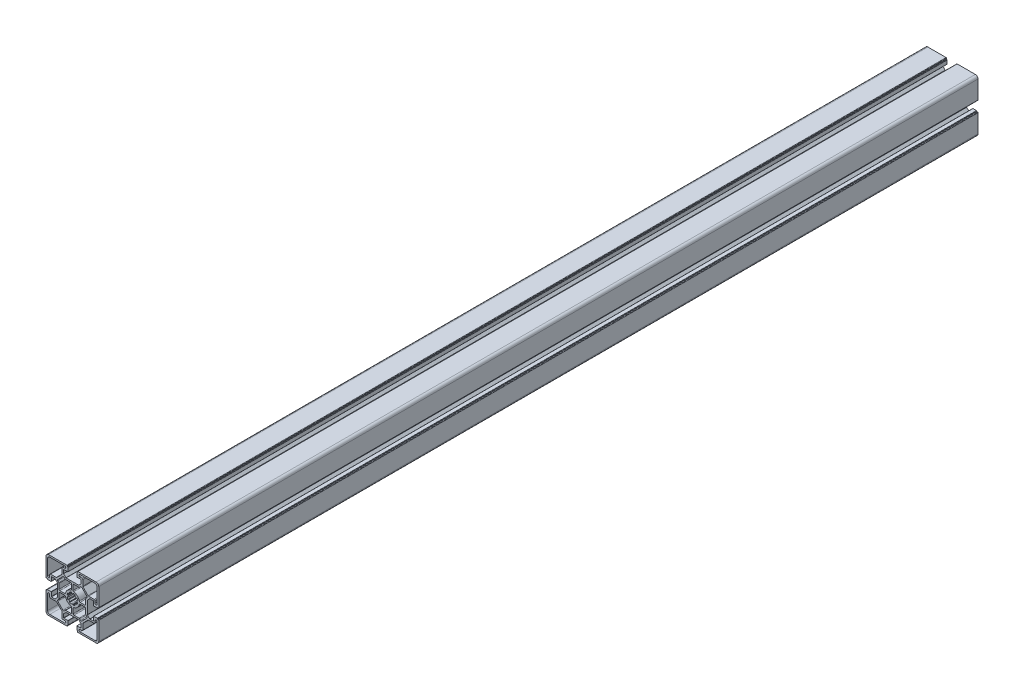
SolidWorks part; units mm, degrees
material "АД31 ГОСТ 4784-97"
ref_plane "Спереди" through (0, 0, 0) normal (0, 0, 1) x (1, 0, 0)
ref_plane "Сверху" through (0, 0, 0) normal (0, 1, 0) x (1, 0, 0)
ref_plane "Справа" through (0, 0, 0) normal (1, 0, 0) x (0, 0, -1)
sketch "Эскиз1" plane through (0, 0, 0) normal (0, 0, 1) x (1, 0, 0)
  line L0 (16.1477, -4.2469) -> (16.1477, 1.4345)
  line L1 (17.495, 3.196) -> (16.4406, 2.1416)
  line L2 (17.495, 4.6102) -> (11.7048, 10.4004)
  line L3 (9.2362, 9.346) -> (10.2906, 10.4004)
  line L4 (8.529, 9.0531) -> (2.8477, 9.0531)
  line L5 (1.8477, 2.6503) -> (1.8477, 8.0531)
  line L6 (15.1477, -5.2469) -> (9.7448, -5.2469)
  line L7 (25.7477, 5.7031) -> (19.3619, 5.7031)
  line L8 (18.6548, 5.996) -> (13.0906, 11.5602)
  line L9 (12.7977, 12.2673) -> (12.7977, 18.6531)
  line L10 (11.7977, 19.6531) -> (9.6477, 19.6531)
  line L11 (26.6477, 22.0531) -> (9.6477, 22.0531)
  line L12 (29.1477, 2.5531) -> (29.1477, 19.5531)
  line L13 (26.7477, 2.5531) -> (26.7477, 4.7031)
  line L14 (6.4406, -5.1783) -> (5.8717, -5.2786)
  line L15 (5.0434, -3.279) -> (5.5166, -2.9477)
  line L16 (4.1469, -1.578) -> (3.8156, -2.0511)
  line L17 (1.9162, -0.654) -> (1.8159, -1.2228)
  line L18 (10.9391, 13.5945) -> (8.2563, 10.9117)
  line L19 (10.9977, 13.736) -> (10.9977, 17.6531)
  line L20 (-16.0523, -13.314) -> (-16.0523, 1.0203)
  line L21 (-16.1109, 1.1617) -> (-18.7937, 3.8445)
  line L22 (-22.8523, 3.9031) -> (-18.9352, 3.9031)
  line L23 (-23.0523, -0.9469) -> (-23.0523, 3.7031)
  line L24 (-23.2523, -1.1469) -> (-27.2523, -1.1469)
  line L25 (-27.5523, -0.8469) -> (-27.5523, -0.6469)
  line L26 (-28.5523, -0.3469) -> (-27.8523, -0.3469)
  line L27 (-29.0523, 0.1531) -> (-29.0523, 20.8531)
  line L28 (-26.0523, 23.8531) -> (-5.3523, 23.8531)
  line L29 (-4.8523, 22.6531) -> (-4.8523, 23.3531)
  line L30 (-4.5523, 22.3531) -> (-4.3523, 22.3531)
  line L31 (-4.0523, 18.0531) -> (-4.0523, 22.0531)
  line L32 (-8.9023, 17.8531) -> (-4.2523, 17.8531)
  line L33 (-9.1023, 13.736) -> (-9.1023, 17.6531)
  line L34 (-9.0438, 13.5945) -> (-6.3609, 10.9117)
  line L35 (-6.2195, 10.8531) -> (8.1148, 10.8531)
  line L36 (10.7977, 17.8531) -> (6.1477, 17.8531)
  line L37 (5.9477, 18.0531) -> (5.9477, 22.0531)
  line L38 (6.4477, 22.3531) -> (6.2477, 22.3531)
  line L39 (6.7477, 22.6531) -> (6.7477, 23.3531)
  line L40 (27.9477, 23.8531) -> (7.2477, 23.8531)
  line L41 (30.9477, 0.1531) -> (30.9477, 20.8531)
  line L42 (30.4477, -0.3469) -> (29.7477, -0.3469)
  line L43 (29.4477, -0.8469) -> (29.4477, -0.6469)
  line L44 (25.1477, -1.1469) -> (29.1477, -1.1469)
  line L45 (24.9477, -0.9469) -> (24.9477, 3.7031)
  line L46 (24.7477, 3.9031) -> (20.8305, 3.9031)
  line L47 (18.0063, 1.1617) -> (20.6891, 3.8445)
  line L48 (17.9477, -13.314) -> (17.9477, 1.0203)
  line L49 (-14.2523, -8.0469) -> (-14.2523, -13.7282)
  line L50 (-15.5996, -15.4897) -> (-14.5452, -14.4353)
  line L51 (-15.5996, -16.904) -> (-9.8094, -22.6942)
  line L52 (-7.3408, -21.6397) -> (-8.3952, -22.6942)
  line L53 (-6.6337, -21.3469) -> (-0.9523, -21.3469)
  line L54 (0.0477, -14.944) -> (0.0477, -20.3469)
  line L55 (-13.2523, -7.0469) -> (-7.8495, -7.0469)
  line L56 (-23.8523, -17.9969) -> (-17.4665, -17.9969)
  line L57 (-16.7594, -18.2898) -> (-11.1952, -23.854)
  line L58 (-10.9023, -24.5611) -> (-10.9023, -30.9469)
  line L59 (-9.9023, -31.9469) -> (-7.7523, -31.9469)
  line L60 (-0.0209, -0.654) -> (0.0794, -1.2228)
  line L61 (-2.2515, -1.578) -> (-1.9202, -2.0511)
  line L62 (-3.1481, -3.279) -> (-3.6212, -2.9477)
  line L63 (-4.5452, -5.1783) -> (-3.9764, -5.2786)
  line L64 (-24.7523, -34.3469) -> (-7.7523, -34.3469)
  line L65 (-27.2523, -14.8469) -> (-27.2523, -31.8469)
  line L66 (-24.8523, -14.8469) -> (-24.8523, -16.9969)
  line L67 (-4.5452, -7.1154) -> (-3.9764, -7.0151)
  line L68 (-3.1481, -9.0147) -> (-3.6212, -9.3461)
  line L69 (-2.2515, -10.7158) -> (-1.9202, -10.2426)
  line L70 (-0.0209, -11.6397) -> (0.0794, -11.0709)
  line L71 (18.0063, -13.4554) -> (20.6891, -16.1383)
  line L72 (24.7477, -16.1968) -> (20.8305, -16.1968)
  line L73 (24.9477, -11.3468) -> (24.9477, -15.9968)
  line L74 (25.1477, -11.1468) -> (29.1477, -11.1468)
  line L75 (29.4477, -11.4468) -> (29.4477, -11.6468)
  line L76 (30.4477, -11.9468) -> (29.7477, -11.9468)
  line L77 (30.9477, -12.4468) -> (30.9477, -33.1468)
  line L78 (27.9477, -36.1468) -> (7.2477, -36.1468)
  line L79 (6.7477, -34.9468) -> (6.7477, -35.6468)
  line L80 (6.4477, -34.6468) -> (6.2477, -34.6468)
  line L81 (5.9477, -30.3468) -> (5.9477, -34.3468)
  line L82 (10.7977, -30.1468) -> (6.1477, -30.1468)
  line L83 (-6.2195, -23.1468) -> (8.1148, -23.1468)
  line L84 (-9.0438, -25.8883) -> (-6.3609, -23.2054)
  line L85 (-9.1023, -26.0297) -> (-9.1023, -29.9468)
  line L86 (-8.9023, -30.1468) -> (-4.2523, -30.1468)
  line L87 (-4.0523, -30.3468) -> (-4.0523, -34.3468)
  line L88 (-4.5523, -34.6468) -> (-4.3523, -34.6468)
  line L89 (-4.8523, -34.9468) -> (-4.8523, -35.6468)
  line L90 (-26.0523, -36.1468) -> (-5.3523, -36.1468)
  line L91 (-29.0523, -12.4468) -> (-29.0523, -33.1468)
  line L92 (-28.5523, -11.9468) -> (-27.8523, -11.9468)
  line L93 (-27.5523, -11.4468) -> (-27.5523, -11.6468)
  line L94 (-23.2523, -11.1468) -> (-27.2523, -11.1468)
  line L95 (-23.0523, -11.3468) -> (-23.0523, -15.9968)
  line L96 (-22.8523, -16.1968) -> (-18.9352, -16.1968)
  line L97 (-16.1109, -13.4554) -> (-18.7937, -16.1383)
  line L98 (10.9977, -26.0297) -> (10.9977, -29.9468)
  line L99 (10.9391, -25.8883) -> (8.2563, -23.2054)
  line L100 (1.9162, -11.6397) -> (1.8159, -11.0709)
  line L101 (4.1469, -10.7158) -> (3.8156, -10.2426)
  line L102 (5.0434, -9.0147) -> (5.5166, -9.3461)
  line L103 (6.4406, -7.1154) -> (5.8717, -7.0151)
  line L104 (-24.8523, 2.5531) -> (-24.8523, 4.7031)
  line L105 (-27.2523, 2.5531) -> (-27.2523, 19.5531)
  line L106 (-24.7523, 22.0531) -> (-7.7523, 22.0531)
  line L107 (-9.9023, 19.6531) -> (-7.7523, 19.6531)
  line L108 (-10.9023, 12.2673) -> (-10.9023, 18.6531)
  line L109 (-16.7594, 5.996) -> (-11.1952, 11.5602)
  line L110 (-23.8523, 5.7031) -> (-17.4665, 5.7031)
  line L111 (26.7477, -14.8469) -> (26.7477, -16.9969)
  line L112 (29.1477, -14.8469) -> (29.1477, -31.8469)
  line L113 (26.6477, -34.3469) -> (9.6477, -34.3469)
  line L114 (11.7977, -31.9469) -> (9.6477, -31.9469)
  line L115 (12.7977, -24.5611) -> (12.7977, -30.9469)
  line L116 (18.6548, -18.2898) -> (13.0906, -23.854)
  line L117 (25.7477, -17.9969) -> (19.3619, -17.9969)
  line L118 (-13.2523, -5.2469) -> (-7.8495, -5.2469)
  line L119 (0.0477, 2.6503) -> (0.0477, 8.0531)
  line L120 (-6.6337, 9.0531) -> (-0.9523, 9.0531)
  line L121 (-7.3408, 9.346) -> (-8.3952, 10.4004)
  line L122 (-15.5996, 4.6102) -> (-9.8094, 10.4004)
  line L123 (-15.5996, 3.196) -> (-14.5452, 2.1416)
  line L124 (-14.2523, -4.2469) -> (-14.2523, 1.4345)
  line L125 (15.1477, -7.0469) -> (9.7448, -7.0469)
  line L126 (1.8477, -14.944) -> (1.8477, -20.3469)
  line L127 (8.529, -21.3469) -> (2.8477, -21.3469)
  line L128 (9.2362, -21.6397) -> (10.2906, -22.6942)
  line L129 (17.495, -16.904) -> (11.7048, -22.6942)
  line L130 (17.495, -15.4897) -> (16.4406, -14.4353)
  line L131 (16.1477, -8.0469) -> (16.1477, -13.7282)
  line L132 (0.9477, -6.1469) -> (0.9477, -46.3575) construction
  line L133 (0.9477, -6.1469) -> (0.9477, 45.0283) construction
  line L134 (0.9477, -6.1469) -> (50.4915, -6.1469) construction
  line L135 (0.9477, -6.1469) -> (-49.7618, -6.1469) construction
  arc A0 (16.1477, -4.2469) -> (15.1477, -5.2469) centre (15.1477, -4.2469) cw
  arc A1 (16.1477, 1.4345) -> (16.4406, 2.1416) centre (17.1477, 1.4345) cw
  arc A2 (17.495, 4.6102) -> (17.495, 3.196) centre (16.7879, 3.9031) cw
  arc A3 (10.2906, 10.4004) -> (11.7048, 10.4004) centre (10.9977, 9.6933) cw
  arc A4 (9.2362, 9.346) -> (8.529, 9.0531) centre (8.529, 10.0531) cw
  arc A5 (1.8477, 8.0531) -> (2.8477, 9.0531) centre (2.8477, 8.0531) cw
  arc A6 (2.6366, 1.6728) -> (1.8477, 2.6503) centre (2.8477, 2.6503) cw
  arc A7 (2.6366, 1.6728) -> (8.7674, -4.458) centre (0.9477, -6.1469) cw
  arc A8 (9.7448, -5.2469) -> (8.7674, -4.458) centre (9.7448, -4.2469) cw
  arc A9 (25.7477, 5.7031) -> (26.7477, 4.7031) centre (25.7477, 4.7031) cw
  arc A10 (19.3619, 5.7031) -> (18.6548, 5.996) centre (19.3619, 6.7031) cw
  arc A11 (13.0906, 11.5602) -> (12.7977, 12.2673) centre (13.7977, 12.2673) cw
  arc A12 (11.7977, 19.6531) -> (12.7977, 18.6531) centre (11.7977, 18.6531) cw
  arc A13 (9.6477, 19.6531) -> (9.6477, 22.0531) centre (9.6477, 20.8531) cw
  arc A14 (26.6477, 22.0531) -> (29.1477, 19.5531) centre (26.6477, 19.5531) cw
  arc A15 (29.1477, 2.5531) -> (26.7477, 2.5531) centre (27.9477, 2.5531) cw
  arc A16 (0.9477, -1.1469) -> (1.8159, -1.2228) centre (0.9477, -6.1469) cw
  arc A17 (5.8717, -5.2786) -> (5.9477, -6.1469) centre (0.9477, -6.1469) cw
  arc A18 (6.8364, -4.5555) -> (6.4406, -5.1783) centre (6.3537, -4.6859) cw
  arc A19 (6.2369, -3.1082) -> (6.8364, -4.5555) centre (0.9477, -6.1469) cw
  arc A20 (-16.0523, 1.0203) -> (-16.1109, 1.1617) centre (-16.2523, 1.0203) ccw
  arc A21 (-18.7937, 3.8445) -> (-18.9352, 3.9031) centre (-18.9352, 3.7031) ccw
  arc A22 (-22.8523, 3.9031) -> (-23.0523, 3.7031) centre (-22.8523, 3.7031) ccw
  arc A23 (-23.2523, -1.1469) -> (-23.0523, -0.9469) centre (-23.2523, -0.9469) ccw
  arc A24 (-27.5523, -0.8469) -> (-27.2523, -1.1469) centre (-27.2523, -0.8469) ccw
  arc A25 (-27.5523, -0.6469) -> (-27.8523, -0.3469) centre (-27.8523, -0.6469) ccw
  arc A26 (-29.0523, 0.1531) -> (-28.5523, -0.3469) centre (-28.5523, 0.1531) ccw
  arc A27 (-26.0523, 23.8531) -> (-29.0523, 20.8531) centre (-26.0523, 20.8531) ccw
  arc A28 (-4.8523, 23.3531) -> (-5.3523, 23.8531) centre (-5.3523, 23.3531) ccw
  arc A29 (-4.8523, 22.6531) -> (-4.5523, 22.3531) centre (-4.5523, 22.6531) ccw
  arc A30 (-4.0523, 22.0531) -> (-4.3523, 22.3531) centre (-4.3523, 22.0531) ccw
  arc A31 (-4.2523, 17.8531) -> (-4.0523, 18.0531) centre (-4.2523, 18.0531) ccw
  arc A32 (-8.9023, 17.8531) -> (-9.1023, 17.6531) centre (-8.9023, 17.6531) ccw
  arc A33 (-9.1023, 13.736) -> (-9.0438, 13.5945) centre (-8.9023, 13.736) ccw
  arc A34 (-6.3609, 10.9117) -> (-6.2195, 10.8531) centre (-6.2195, 11.0531) ccw
  arc A35 (5.5166, -2.9477) -> (6.2369, -3.1082) centre (5.8034, -3.3572) cw
  arc A36 (3.8156, -2.0511) -> (5.0434, -3.279) centre (0.9477, -6.1469) cw
  arc A37 (3.9864, -0.8576) -> (4.1469, -1.578) centre (3.7373, -1.2912) cw
  arc A38 (2.5391, -0.2581) -> (3.9864, -0.8576) centre (0.9477, -6.1469) cw
  arc A39 (1.9162, -0.654) -> (2.5391, -0.2581) centre (2.4086, -0.7408) cw
  arc A40 (8.2563, 10.9117) -> (8.1148, 10.8531) centre (8.1148, 11.0531) cw
  arc A41 (10.9977, 13.736) -> (10.9391, 13.5945) centre (10.7977, 13.736) cw
  arc A42 (10.7977, 17.8531) -> (10.9977, 17.6531) centre (10.7977, 17.6531) cw
  arc A43 (6.1477, 17.8531) -> (5.9477, 18.0531) centre (6.1477, 18.0531) cw
  arc A44 (5.9477, 22.0531) -> (6.2477, 22.3531) centre (6.2477, 22.0531) cw
  arc A45 (6.7477, 22.6531) -> (6.4477, 22.3531) centre (6.4477, 22.6531) cw
  arc A46 (6.7477, 23.3531) -> (7.2477, 23.8531) centre (7.2477, 23.3531) cw
  arc A47 (27.9477, 23.8531) -> (30.9477, 20.8531) centre (27.9477, 20.8531) cw
  arc A48 (30.9477, 0.1531) -> (30.4477, -0.3469) centre (30.4477, 0.1531) cw
  arc A49 (29.4477, -0.6469) -> (29.7477, -0.3469) centre (29.7477, -0.6469) cw
  arc A50 (29.4477, -0.8469) -> (29.1477, -1.1469) centre (29.1477, -0.8469) cw
  arc A51 (25.1477, -1.1469) -> (24.9477, -0.9469) centre (25.1477, -0.9469) cw
  arc A52 (24.7477, 3.9031) -> (24.9477, 3.7031) centre (24.7477, 3.7031) cw
  arc A53 (20.6891, 3.8445) -> (20.8305, 3.9031) centre (20.8305, 3.7031) cw
  arc A54 (17.9477, 1.0203) -> (18.0063, 1.1617) centre (18.1477, 1.0203) cw
  arc A55 (-14.2523, -8.0469) -> (-13.2523, -7.0469) centre (-13.2523, -8.0469) cw
  arc A56 (-14.2523, -13.7282) -> (-14.5452, -14.4353) centre (-15.2523, -13.7282) cw
  arc A57 (-15.5996, -16.904) -> (-15.5996, -15.4897) centre (-14.8925, -16.1969) cw
  arc A58 (-8.3952, -22.6942) -> (-9.8094, -22.6942) centre (-9.1023, -21.9871) cw
  arc A59 (-7.3408, -21.6397) -> (-6.6337, -21.3469) centre (-6.6337, -22.3469) cw
  arc A60 (-0.0209, -0.654) -> (-0.6437, -0.2581) centre (-0.5133, -0.7408) ccw
  arc A61 (-0.6437, -0.2581) -> (-2.091, -0.8576) centre (0.9477, -6.1469) ccw
  arc A62 (-2.091, -0.8576) -> (-2.2515, -1.578) centre (-1.842, -1.2912) ccw
  arc A63 (-1.9202, -2.0511) -> (-3.1481, -3.279) centre (0.9477, -6.1469) ccw
  arc A64 (-3.6212, -2.9477) -> (-4.3416, -3.1082) centre (-3.908, -3.3572) ccw
  arc A65 (-4.3416, -3.1082) -> (-4.9411, -4.5555) centre (0.9477, -6.1469) ccw
  arc A66 (-4.9411, -4.5555) -> (-4.5452, -5.1783) centre (-4.4584, -4.6859) ccw
  arc A67 (-3.9764, -5.2786) -> (-4.0523, -6.1469) centre (0.9477, -6.1469) ccw
  arc A68 (0.0477, -20.3469) -> (-0.9523, -21.3469) centre (-0.9523, -20.3469) cw
  arc A69 (-0.7412, -13.9666) -> (0.0477, -14.944) centre (-0.9523, -14.944) cw
  arc A70 (-0.7412, -13.9666) -> (-6.872, -7.8357) centre (0.9477, -6.1469) cw
  arc A71 (-7.8495, -7.0469) -> (-6.872, -7.8357) centre (-7.8495, -8.0469) cw
  arc A72 (-23.8523, -17.9969) -> (-24.8523, -16.9969) centre (-23.8523, -16.9969) cw
  arc A73 (-17.4665, -17.9969) -> (-16.7594, -18.2898) centre (-17.4665, -18.9969) cw
  arc A74 (-11.1952, -23.854) -> (-10.9023, -24.5611) centre (-11.9023, -24.5611) cw
  arc A75 (-9.9023, -31.9469) -> (-10.9023, -30.9469) centre (-9.9023, -30.9469) cw
  arc A76 (-7.7523, -31.9469) -> (-7.7523, -34.3469) centre (-7.7523, -33.1469) cw
  arc A77 (-24.7523, -34.3469) -> (-27.2523, -31.8469) centre (-24.7523, -31.8469) cw
  arc A78 (-27.2523, -14.8469) -> (-24.8523, -14.8469) centre (-26.0523, -14.8469) cw
  arc A79 (0.9477, -11.1469) -> (0.0794, -11.0709) centre (0.9477, -6.1468) cw
  arc A80 (-3.9764, -7.0151) -> (-4.0523, -6.1469) centre (0.9477, -6.1468) cw
  arc A81 (-4.9411, -7.7383) -> (-4.5452, -7.1154) centre (-4.4584, -7.6078) cw
  arc A82 (-4.3416, -9.1856) -> (-4.9411, -7.7383) centre (0.9477, -6.1469) cw
  arc A83 (-3.6212, -9.3461) -> (-4.3416, -9.1856) centre (-3.908, -8.9365) cw
  arc A84 (-1.9202, -10.2426) -> (-3.1481, -9.0147) centre (0.9477, -6.1468) cw
  arc A85 (-2.091, -11.4361) -> (-2.2515, -10.7158) centre (-1.842, -11.0026) cw
  arc A86 (-0.6437, -12.0356) -> (-2.091, -11.4361) centre (0.9477, -6.1469) cw
  arc A87 (-0.0209, -11.6397) -> (-0.6437, -12.0356) centre (-0.5133, -11.5529) cw
  arc A88 (17.9477, -13.314) -> (18.0063, -13.4554) centre (18.1477, -13.314) ccw
  arc A89 (20.6891, -16.1383) -> (20.8305, -16.1968) centre (20.8305, -15.9968) ccw
  arc A90 (24.7477, -16.1968) -> (24.9477, -15.9968) centre (24.7477, -15.9968) ccw
  arc A91 (0.9477, -1.1469) -> (0.0794, -1.2228) centre (0.9477, -6.1469) ccw
  arc A92 (25.1477, -11.1468) -> (24.9477, -11.3468) centre (25.1477, -11.3468) ccw
  arc A93 (29.4477, -11.4468) -> (29.1477, -11.1468) centre (29.1477, -11.4468) ccw
  arc A94 (29.4477, -11.6468) -> (29.7477, -11.9468) centre (29.7477, -11.6468) ccw
  arc A95 (30.9477, -12.4468) -> (30.4477, -11.9468) centre (30.4477, -12.4468) ccw
  arc A96 (27.9477, -36.1468) -> (30.9477, -33.1468) centre (27.9477, -33.1468) ccw
  arc A97 (6.7477, -35.6468) -> (7.2477, -36.1468) centre (7.2477, -35.6468) ccw
  arc A98 (6.7477, -34.9468) -> (6.4477, -34.6468) centre (6.4477, -34.9468) ccw
  arc A99 (5.9477, -34.3468) -> (6.2477, -34.6468) centre (6.2477, -34.3468) ccw
  arc A100 (6.1477, -30.1468) -> (5.9477, -30.3468) centre (6.1477, -30.3468) ccw
  arc A101 (10.7977, -30.1468) -> (10.9977, -29.9468) centre (10.7977, -29.9468) ccw
  arc A102 (10.9977, -26.0297) -> (10.9391, -25.8883) centre (10.7977, -26.0297) ccw
  arc A103 (8.2563, -23.2054) -> (8.1148, -23.1468) centre (8.1148, -23.3468) ccw
  arc A104 (1.9162, -11.6397) -> (2.5391, -12.0356) centre (2.4086, -11.5529) ccw
  arc A105 (2.5391, -12.0356) -> (3.9864, -11.4361) centre (0.9477, -6.1469) ccw
  arc A106 (3.9864, -11.4361) -> (4.1469, -10.7158) centre (3.7373, -11.0026) ccw
  arc A107 (3.8156, -10.2426) -> (5.0434, -9.0147) centre (0.9477, -6.1468) ccw
  arc A108 (5.5166, -9.3461) -> (6.2369, -9.1856) centre (5.8034, -8.9365) ccw
  arc A109 (-6.3609, -23.2054) -> (-6.2195, -23.1468) centre (-6.2195, -23.3468) cw
  arc A110 (-9.1023, -26.0297) -> (-9.0438, -25.8883) centre (-8.9023, -26.0297) cw
  arc A111 (-8.9023, -30.1468) -> (-9.1023, -29.9468) centre (-8.9023, -29.9468) cw
  arc A112 (-4.2523, -30.1468) -> (-4.0523, -30.3468) centre (-4.2523, -30.3468) cw
  arc A113 (-4.0523, -34.3468) -> (-4.3523, -34.6468) centre (-4.3523, -34.3468) cw
  arc A114 (-4.8523, -34.9468) -> (-4.5523, -34.6468) centre (-4.5523, -34.9468) cw
  arc A115 (-4.8523, -35.6468) -> (-5.3523, -36.1468) centre (-5.3523, -35.6468) cw
  arc A116 (-26.0523, -36.1468) -> (-29.0523, -33.1468) centre (-26.0523, -33.1468) cw
  arc A117 (-29.0523, -12.4468) -> (-28.5523, -11.9468) centre (-28.5523, -12.4468) cw
  arc A118 (-27.5523, -11.6468) -> (-27.8523, -11.9468) centre (-27.8523, -11.6468) cw
  arc A119 (-27.5523, -11.4468) -> (-27.2523, -11.1468) centre (-27.2523, -11.4468) cw
  arc A120 (-23.2523, -11.1468) -> (-23.0523, -11.3468) centre (-23.2523, -11.3468) cw
  arc A121 (-22.8523, -16.1968) -> (-23.0523, -15.9968) centre (-22.8523, -15.9968) cw
  arc A122 (-18.7937, -16.1383) -> (-18.9352, -16.1968) centre (-18.9352, -15.9968) cw
  arc A123 (-16.0523, -13.314) -> (-16.1109, -13.4554) centre (-16.2523, -13.314) cw
  arc A124 (-27.2523, 2.5531) -> (-24.8523, 2.5531) centre (-26.0523, 2.5531) ccw
  arc A125 (-24.7523, 22.0531) -> (-27.2523, 19.5531) centre (-24.7523, 19.5531) ccw
  arc A126 (-7.7523, 19.6531) -> (-7.7523, 22.0531) centre (-7.7523, 20.8531) ccw
  arc A127 (-9.9023, 19.6531) -> (-10.9023, 18.6531) centre (-9.9023, 18.6531) ccw
  arc A128 (-11.1952, 11.5602) -> (-10.9023, 12.2673) centre (-11.9023, 12.2673) ccw
  arc A129 (-17.4665, 5.7031) -> (-16.7594, 5.996) centre (-17.4665, 6.7031) ccw
  arc A130 (-23.8523, 5.7031) -> (-24.8523, 4.7031) centre (-23.8523, 4.7031) ccw
  arc A131 (6.2369, -9.1856) -> (6.8364, -7.7383) centre (0.9477, -6.1469) ccw
  arc A132 (6.8364, -7.7383) -> (6.4406, -7.1154) centre (6.3537, -7.6078) ccw
  arc A133 (5.8717, -7.0151) -> (5.9477, -6.1469) centre (0.9477, -6.1468) ccw
  arc A134 (0.9477, -11.1469) -> (1.8159, -11.0709) centre (0.9477, -6.1468) ccw
  arc A135 (29.1477, -14.8469) -> (26.7477, -14.8469) centre (27.9477, -14.8469) ccw
  arc A136 (26.6477, -34.3469) -> (29.1477, -31.8469) centre (26.6477, -31.8469) ccw
  arc A137 (9.6477, -31.9469) -> (9.6477, -34.3469) centre (9.6477, -33.1469) ccw
  arc A138 (-7.8495, -5.2469) -> (-6.872, -4.458) centre (-7.8495, -4.2469) ccw
  arc A139 (-0.7412, 1.6728) -> (-6.872, -4.458) centre (0.9477, -6.1469) ccw
  arc A140 (-0.7412, 1.6728) -> (0.0477, 2.6503) centre (-0.9523, 2.6503) ccw
  arc A141 (0.0477, 8.0531) -> (-0.9523, 9.0531) centre (-0.9523, 8.0531) ccw
  arc A142 (-7.3408, 9.346) -> (-6.6337, 9.0531) centre (-6.6337, 10.0531) ccw
  arc A143 (-8.3952, 10.4004) -> (-9.8094, 10.4004) centre (-9.1023, 9.6933) ccw
  arc A144 (-15.5996, 4.6102) -> (-15.5996, 3.196) centre (-14.8925, 3.9031) ccw
  arc A145 (-14.2523, 1.4345) -> (-14.5452, 2.1416) centre (-15.2523, 1.4345) ccw
  arc A146 (-14.2523, -4.2469) -> (-13.2523, -5.2469) centre (-13.2523, -4.2469) ccw
  arc A147 (11.7977, -31.9469) -> (12.7977, -30.9469) centre (11.7977, -30.9469) ccw
  arc A148 (13.0906, -23.854) -> (12.7977, -24.5611) centre (13.7977, -24.5611) ccw
  arc A149 (19.3619, -17.9969) -> (18.6548, -18.2898) centre (19.3619, -18.9969) ccw
  arc A150 (25.7477, -17.9969) -> (26.7477, -16.9969) centre (25.7477, -16.9969) ccw
  arc A151 (9.7448, -7.0469) -> (8.7674, -7.8357) centre (9.7448, -8.0469) ccw
  arc A152 (2.6366, -13.9666) -> (8.7674, -7.8357) centre (0.9477, -6.1469) ccw
  arc A153 (2.6366, -13.9666) -> (1.8477, -14.944) centre (2.8477, -14.944) ccw
  arc A154 (1.8477, -20.3469) -> (2.8477, -21.3469) centre (2.8477, -20.3469) ccw
  arc A155 (9.2362, -21.6397) -> (8.529, -21.3469) centre (8.529, -22.3469) ccw
  arc A156 (10.2906, -22.6942) -> (11.7048, -22.6942) centre (10.9977, -21.9871) ccw
  arc A157 (17.495, -16.904) -> (17.495, -15.4897) centre (16.7879, -16.1969) ccw
  arc A158 (16.1477, -13.7282) -> (16.4406, -14.4353) centre (17.1477, -13.7282) ccw
  arc A159 (16.1477, -8.0469) -> (15.1477, -7.0469) centre (15.1477, -8.0469) ccw
  point P124 (0.9477, 10.8531)
  point P125 (-16.0523, -6.1469)
  point P439 (0.9477, -23.1468)
  point P440 (17.9477, -6.1469)
  dimension "D6" = 10.0001
  dimension "D1" = 10
  dimension "D2" = 59.9999
  dimension "D3" = 60
  dimension "D4" = 30
  dimension "D5" = 13
extrude "Бобышка-Вытянуть1" add sketch "Эскиз1" along normal blind 1000
